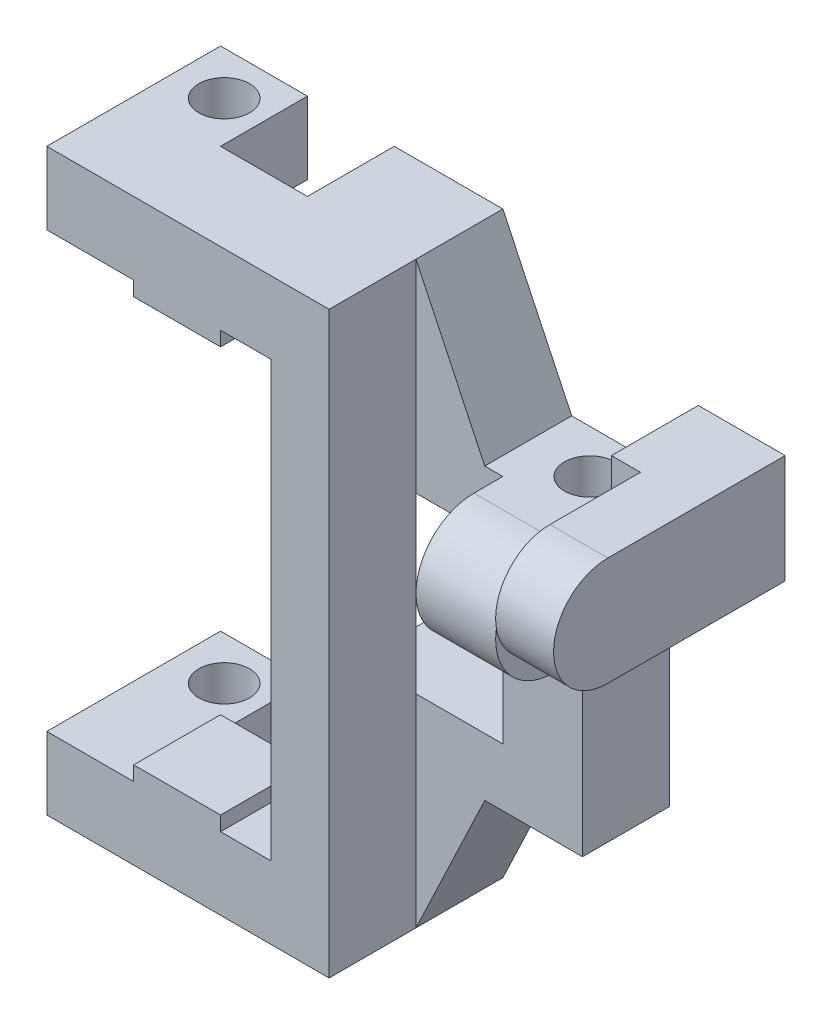
SolidWorks part; units mm, degrees
ref_plane "Front" through (0, 0, 0) normal (0, 0, 1) x (1, 0, 0)
ref_plane "Top" through (0, 0, 0) normal (0, 1, 0) x (1, 0, 0)
ref_plane "Right" through (0, 0, 0) normal (1, 0, 0) x (0, 0, -1)
sketch "Sketch1" plane through (0, 0, 0) normal (0, 0, 1) x (1, 0, 0)
  line L0 (-4, 4) -> (-4, -5)
  line L1 (0, 0) -> (11.5, 0)
  line L3 (0, 20) -> (11.5, 20)
  line L4 (11.5, 0) -> (11.5, 20)
  line L5 (-4, 16) -> (6, 16)
  line L6 (-4, 16) -> (-4, 4)
  line L7 (-4, 4) -> (6, 4)
  line L8 (6, 16) -> (6, 4)
  line L9 (-19.5, -10) -> (-19.5, -5)
  line L10 (-19.5, -5) -> (-4, -5)
  line L11 (-19.5, -10) -> (0, -10)
  line L12 (0, -10) -> (0, 0)
  line L13 (-4, 25) -> (-4, 16)
  line L14 (-19.5, 30) -> (-19.5, 25)
  line L15 (-19.5, 25) -> (-4, 25)
  line L16 (-19.5, 30) -> (0, 30)
  line L17 (0, 30) -> (0, 20)
  line L18 (4.75, 0) -> (0, -10)
  line L19 (4.75, 20) -> (0, 30)
  dimension "D1" = 11.5
  dimension "D4" = 4
  dimension "D6" = 5.5
  dimension "D7" = 5
  dimension "D9" = 15.5
  dimension "D2" = 40
  dimension "D8" = 9
  dimension "D5" = 10
  dimension "D3" = 4
  dimension "D10" = 1.25
extrude "Boss-Extrude1" add sketch "Sketch1" along normal blind 6
sketch "Sketch2" plane through (0, -10, 0) normal (0, -1, 0) x (1, 0, 0)
  line L0 (11.5, 6) -> (11.5, 0) construction
  line L1 (4.75, 0) -> (11.5, 0) construction
  line L7 (-19.5, 6) -> (-19.5, 0) construction
  line L13 (11.5, 6) -> (11.5, 0)
  line L14 (4.75, 0) -> (11.5, 0)
  line L15 (0, 6) -> (11.5, 6)
  line L17 (-19.5, 6) -> (-19.5, 0)
  line L19 (11.5, 3) -> (9, 3)
  line L21 (-19.5, 3) -> (-16.25, 3)
  line L23 (4.75, 0) -> (11.5, 0) construction
  line L24 (4.75, 0) -> (0, 0) construction
  line L25 (4.75, 6) -> (11.5, 6) construction
  line L26 (4.75, 6) -> (0, 6) construction
  line L27 (4.75, 0) -> (11.5, 0)
  line L28 (4.75, 0) -> (0, 0)
  line L29 (4.75, 6) -> (11.5, 6)
  line L30 (4.75, 6) -> (0, 6)
  circle A1 centre (9, 3) radius 1.75
  circle A2 centre (-16.25, 3) radius 1.75
  dimension "D2" = 3.5
  dimension "D1" = 2.5
  dimension "D3" = 3.25
extrude "Cut-Extrude1" cut sketch "Sketch2" against normal through all
ref_plane "Plane1" through (11.5, 0, 0) normal (1, 0, 0) x (0, 0, -1)
sketch "Sketch3" plane through (11.5, 0, 0) normal (1, 0, 0) x (0, 0, -1)
  line L2 (-6, 0) -> (-6, 20) construction
  line L3 (-6, 0) -> (-6, 20)
  line L5 (-6, 20) -> (-8, 20)
  line L6 (-8, 12) -> (-6, 12)
  arc A0 (-8, 20) -> (-8, 12) centre (-8, 16) ccw
  circle A2 centre (-8, 16) radius 1.5
  dimension "D2" = 2
  dimension "D3" = 3
  dimension "D1" = 8
extrude "Boss-Extrude7" add sketch "Sketch3" against normal up to surface (5.5 mm away) contours L5 A0 L6 L3 A2
sketch "Sketch4" plane through (0, 0, 6) normal (0, 0, 1) x (1, 0, 0)
  line L0 (-19.5, -10) -> (0, -10) construction
  line L1 (-19.5, -10) -> (-19.5, -5) construction
  line L2 (-19.5, -5) -> (-4, -5) construction
  line L3 (-19.5, -10) -> (0, -10)
  line L4 (-19.5, -10) -> (-19.5, -5)
  line L5 (-19.5, -5) -> (-4, -5)
  line L6 (-19.5, 25) -> (-4, 25) construction
  line L7 (-19.5, 30) -> (0, 30) construction
  line L8 (-19.5, 30) -> (-19.5, 25) construction
  line L9 (-19.5, 25) -> (-4, 25)
  line L10 (-19.5, 30) -> (0, 30)
  line L11 (-19.5, 30) -> (-19.5, 25)
  line L14 (0, 4) -> (0, 16)
  line L16 (-4, 16) -> (-4, 4)
  line L17 (0, 24) -> (0, 30)
  line L18 (0, 24) -> (0, 16)
  line L19 (-4, 16) -> (6, 16) construction
  line L20 (0, 16) -> (-4, 16)
  line L21 (-4, 16) -> (-4, 25)
  line L23 (-4, 4) -> (6, 4) construction
  line L24 (0, 4) -> (-4, 4)
  line L25 (-4, 4) -> (-4, -5)
  line L26 (0, -10) -> (0, 4)
  line M7 (6, 4) -> (-4, 4)
  line M8 (-4, 4) -> (-4, -5)
  line M9 (-4, -5) -> (-19.5, -5)
  line M10 (-19.5, -5) -> (-19.5, -10)
  line M11 (-19.5, -10) -> (0, -10)
extrude "Boss-Extrude8" add sketch "Sketch4" along normal blind 6 contours L14 L20 L16 M7 | L21 L20 L18 L17 L10 L11 L9 | L26 M11 M7 M8 M9 M10
sketch "Sketch7" plane through (0, -10, 0) normal (0, -1, 0) x (1, 0, 0)
  line L0 (-13.5, 0) -> (-13.5, 6)
  line L1 (-13.5, 6) -> (-7.5, 6)
  line L2 (-7.5, 6) -> (-7.5, 0)
  line L4 (-19.5, 0) -> (0, 0)
  line L5 (0, 0) -> (0, 6)
  line L6 (0, 6) -> (0, 12)
  line L7 (-19.5, 12) -> (-19.5, 0)
  line L8 (-19.5, 0) -> (0, 0)
  line L11 (-19.5, 12) -> (-19.5, 0)
  line L16 (0, 0) -> (0, 6)
  line L23 (0, 6) -> (0, 12)
  line L24 (0, 12) -> (-19.5, 12)
  line L25 (0, 12) -> (-19.5, 12)
  line M8 (-19.5, 0) -> (0, 0)
  dimension "D2" = 6
  dimension "D3" = 6
  dimension "D4" = 6
  dimension "D1" = 0
extrude "Cut-Extrude2" cut sketch "Sketch7" against normal up to surface (40 mm away) contours L2 L1 L0 M8 up to face at (-16.25, 30, 1.25)
sketch "Sketch9" plane through (0, 0, 0) normal (0, 0, -1) x (-1, 0, 0)
  line L0 (-11.5, 0) -> (-11.5, 20) construction
  line L1 (-11.5, 0) -> (-11.5, 20)
  line L2 (-11.5, 20) -> (-13.5, 20)
  line L3 (-13.5, 20) -> (-13.5, 25)
  line L4 (-13.5, 25) -> (-19.5, 25)
  line L5 (-19.5, 25) -> (-19.5, 20)
  line L9 (-11.5, 12) -> (-17.5, 17.5)
  line L10 (-19.5, 20) -> (-19.5, 17.5)
  line L11 (-19.5, 17.5) -> (-17.5, 17.5)
  line M10 (-11.5, 20) -> (-11.5, 0)
  dimension "D1" = 6
  dimension "D2" = 2
  dimension "D3" = 8
  dimension "D4" = 8
  dimension "D5" = 7.5
  dimension "D6" = 5
  dimension "D7" = 2
extrude "Boss-Extrude9" add sketch "Sketch9" against normal up to surface (6 mm away) contours L9 L2 L3 L4 L5 M10 up to face at (3.35, 20.4, 6)
sketch "Sketch10" plane through (0, 0, 6) normal (0, 0, 1) x (1, 0, 0)
  line L0 (15.5, 25) -> (15.5, 15.6667)
  line L1 (13.5, 25) -> (19.5, 25) construction
  line L2 (11.5, 12) -> (17.5, 17.5) construction
  line L4 (13.5, 25) -> (19.5, 25)
  line L5 (17, 17.5) -> (19.5, 17.5)
  line L7 (11.5, 20) -> (11.5, 12) construction
  line L8 (11.5, 20) -> (11.5, 12)
  line L9 (15.5, 17.5) -> (17, 17.5)
  line L11 (11.5, 20) -> (13.5, 20) construction
  line L12 (15.5, 25) -> (19.5, 25)
  dimension "D1" = 4
  dimension "D2" = 2.5
extrude "Boss-Extrude10" add sketch "Sketch10" along normal blind 10
sketch "Sketch11" plane through (19.5, 0, 0) normal (1, 0, 0) x (0, 0, -1)
  line L0 (-16, 25) -> (0, 25) construction
  line L1 (-16, 17.5) -> (-16, 25) construction
  line L2 (-16, 17.5) -> (0, 17.5) construction
  line L3 (-16, 25) -> (0, 25)
  line L4 (0, 25) -> (-16, 25)
  line L5 (-16, 25) -> (-16, 17.5)
  line L6 (-16, 17.5) -> (-16, 25)
  line L7 (0, 17.5) -> (0, 25)
  line L11 (0, 17.5) -> (0, 25)
  line L12 (-16, 17.5) -> (0, 17.5)
  line L21 (-16, 17.5) -> (0, 17.5)
  arc A0 (-12.25, 25) -> (-12.25, 17.5) centre (-12.25, 21.25) ccw
  dimension "D1" = 0
extrude "Cut-Extrude3" cut sketch "Sketch11" against normal up to next
sketch "Sketch12" plane through (0, 25, 0) normal (0, -1, 0) x (1, 0, 0)
  line L0 (-7.5, 6) -> (-7.5, 12)
  line L1 (-19.5, 12) -> (-4, 12) construction
  line L2 (-13.5, 6) -> (-13.5, 12)
  line L3 (-7.5, 6) -> (-13.5, 6) construction
  line L4 (-7.5, 6) -> (-13.5, 6)
  line L5 (-19.5, 12) -> (-4, 12)
  line M5 (-4, 12) -> (-19.5, 12)
  line M9 (-13.5, 6) -> (-7.5, 6)
extrude "Boss-Extrude11" add sketch "Sketch12" along normal blind 1 contours L2 L0 M9 M5
sketch "Sketch13" plane through (0, -5, 0) normal (0, 1, 0) x (1, 0, 0)
  line L0 (-7.5, -6) -> (-7.5, -12)
  line L1 (-4, -12) -> (-19.5, -12) construction
  line L2 (-13.5, -6) -> (-13.5, -12)
  line L3 (-7.5, -6) -> (-13.5, -6) construction
  line L4 (-7.5, -6) -> (-13.5, -6)
  line L5 (-4, -12) -> (-19.5, -12)
  line M4 (-7.5, -6) -> (-13.5, -6)
  line M8 (-19.5, -12) -> (-4, -12)
extrude "Boss-Extrude12" add sketch "Sketch13" along normal blind 1 contours L2 L0 M4 M8
equation "\"D3@Sketch1\"=\"D4@Sketch1\""
equation "\"D4@Sketch9\"=\"D3@Sketch9\""
